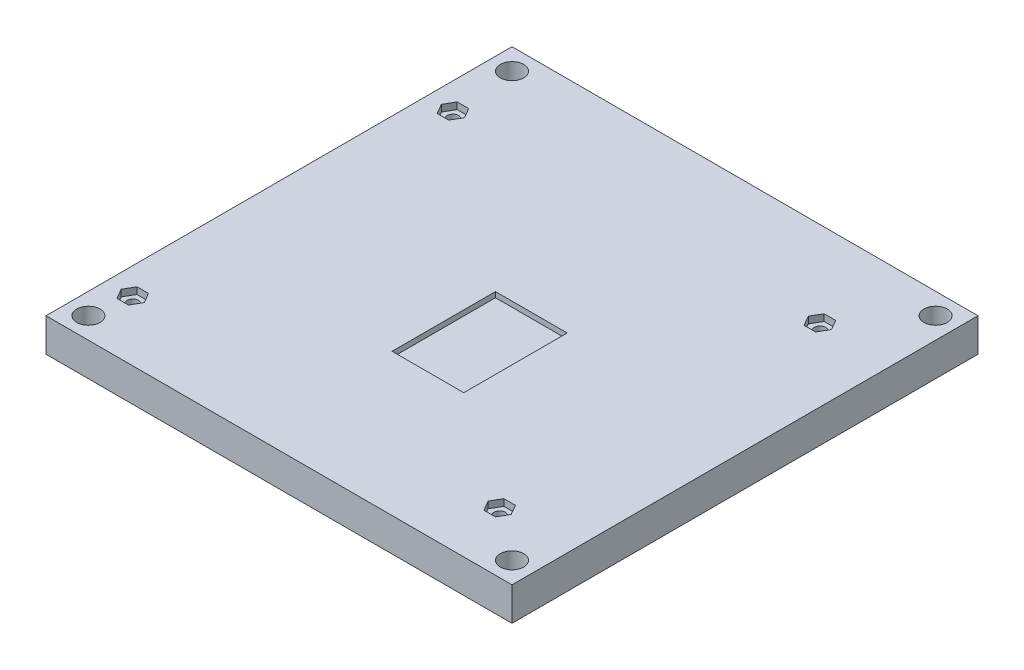
SolidWorks part; units mm, degrees
ref_plane "Front Plane" through (0, 0, 0) normal (0, 0, 1) x (1, 0, 0)
ref_plane "Top Plane" through (0, 0, 0) normal (0, 1, 0) x (1, 0, 0)
ref_plane "Right Plane" through (0, 0, 0) normal (1, 0, 0) x (0, 0, -1)
sketch "Sketch2" plane through (0, 0, 0) normal (0, 1, 0) x (1, 0, 0)
  line L1 (0, 0) -> (139.7, 0)
  line L2 (0, 0) -> (0, 139.7)
  line L3 (0, 139.7) -> (139.7, 139.7)
  line L4 (139.7, 0) -> (139.7, 139.7)
  dimension "D1" = 139.7
  dimension "D2" = 139.7
extrude "Boss-Extrude1" add sketch "Sketch2" along normal blind 10
sketch "Sketch1" plane through (0, 10, 0) normal (0, 1, 0) x (1, 0, 0)
  line L0 (139.7, 139.7) -> (0, 139.7) construction
  line L5 (6.35, 133.35) -> (133.35, 133.35) construction
  line L6 (6.35, 133.35) -> (6.35, 6.35) construction
  line L7 (6.35, 6.35) -> (133.35, 6.35) construction
  line L8 (133.35, 133.35) -> (133.35, 6.35) construction
  line L10 (6.35, 133.35) -> (0, 133.35)
  line L11 (0, 139.7) -> (0, 0) construction
  line L12 (6.35, 133.35) -> (6.35, 139.7)
  circle A0 centre (6.35, 6.35) radius 3.5
  circle A1 centre (6.35, 133.35) radius 3.5
  circle A2 centre (133.35, 133.35) radius 3.5
  circle A3 centre (133.35, 6.35) radius 3.5
  point P2 (69.85, 139.7)
  point P3 (69.85, 133.35)
  dimension "D5" = 7
  dimension "D3" = 127
  dimension "D4" = 127
extrude "Cut-Extrude1" cut sketch "Sketch1" against normal blind 10 contours L12 A1 L10 | L10 A1 L12 | A2 | A0 | A3
sketch "Sketch3" plane through (0, 10, 0) normal (0, 1, 0) x (1, 0, 0)
  line L0 (139.7, 139.7) -> (0, 139.7) construction
  line L1 (61.1, 73.6468) -> (82.6, 73.6468)
  line L2 (61.1, 73.6468) -> (61.1, 42.6468)
  line L3 (61.1, 42.6468) -> (82.6, 42.6468)
  line L4 (82.6, 73.6468) -> (82.6, 42.6468)
  circle A0 centre (69.85, 69.6468) radius 2.25 construction
  circle A1 centre (6.35, 133.35) radius 3.5 construction
  point P9 (69.85, 139.7)
  dimension "D4" = 4.5
  dimension "D6" = 63.7032
  dimension "D1" = 21.5
  dimension "D2" = 31
  dimension "D3" = 4
  dimension "D5" = 8.75
extrude "Cut-Extrude2" cut sketch "Sketch3" against normal blind 1.6
sketch "Sketch4" plane through (0, 10, 0) normal (0, 1, 0) x (1, 0, 0)
  circle A0 centre (7.85, 114.1468) radius 1.7
  circle A1 centre (7.85, 18.1468) radius 1.7
  circle A2 centre (117.85, 114.1468) radius 1.7
  circle A3 centre (117.85, 18.1468) radius 1.7
  point P8 (0, 0)
  point P9 (0, 0)
  point P10 (0, 0)
  point P11 (0, 0)
  dimension "D1" = 3.4
  dimension "D2" = 96
  dimension "D3" = 110
  dimension "D4" = 44.5
  dimension "D5" = 48
extrude "Cut-Extrude3" cut sketch "Sketch4" against normal blind 10
sketch "Sketch5" plane through (0, 10, 0) normal (0, 1, 0) x (1, 0, 0)
  line L0 (139.7, 139.7) -> (0, 139.7) construction
  line L1 (9.5821, 111.1468) -> (11.3141, 114.1468)
  line L2 (11.3141, 114.1468) -> (9.5821, 117.1468)
  line L3 (9.5821, 117.1468) -> (6.1179, 117.1468)
  line L4 (6.1179, 117.1468) -> (4.3859, 114.1468)
  line L5 (4.3859, 114.1468) -> (6.1179, 111.1468)
  line L6 (6.1179, 111.1468) -> (9.5821, 111.1468)
  line L7 (9.5821, 15.1468) -> (11.3141, 18.1468)
  line L8 (11.3141, 18.1468) -> (9.5821, 21.1468)
  line L9 (9.5821, 21.1468) -> (6.1179, 21.1468)
  line L10 (6.1179, 21.1468) -> (4.3859, 18.1468)
  line L11 (4.3859, 18.1468) -> (6.1179, 15.1468)
  line L12 (6.1179, 15.1468) -> (9.5821, 15.1468)
  line L13 (119.5821, 111.1468) -> (121.3141, 114.1468)
  line L14 (121.3141, 114.1468) -> (119.5821, 117.1468)
  line L15 (119.5821, 117.1468) -> (116.1179, 117.1468)
  line L16 (116.1179, 117.1468) -> (114.3859, 114.1468)
  line L17 (114.3859, 114.1468) -> (116.1179, 111.1468)
  line L18 (116.1179, 111.1468) -> (119.5821, 111.1468)
  line L19 (119.5821, 15.1468) -> (121.3141, 18.1468)
  line L20 (121.3141, 18.1468) -> (119.5821, 21.1468)
  line L21 (119.5821, 21.1468) -> (116.1179, 21.1468)
  line L22 (116.1179, 21.1468) -> (114.3859, 18.1468)
  line L23 (114.3859, 18.1468) -> (116.1179, 15.1468)
  line L24 (116.1179, 15.1468) -> (119.5821, 15.1468)
  line L25 (0, 0) -> (139.7, 0) construction
  circle A0 centre (7.85, 114.1468) radius 3 construction
  circle A1 centre (7.85, 18.1468) radius 3 construction
  circle A2 centre (117.85, 114.1468) radius 3 construction
  circle A3 centre (117.85, 18.1468) radius 3 construction
  circle A4 centre (7.85, 114.1468) radius 1.7 construction
  circle A5 centre (117.85, 114.1468) radius 1.7 construction
  circle A6 centre (7.85, 18.1468) radius 1.7 construction
  circle A7 centre (117.85, 18.1468) radius 1.7 construction
  point P25 (0, 0)
  point P41 (7.85, 111.1468)
  dimension "D1" = 6
extrude "Cut-Extrude4" cut sketch "Sketch5" against normal blind 2
